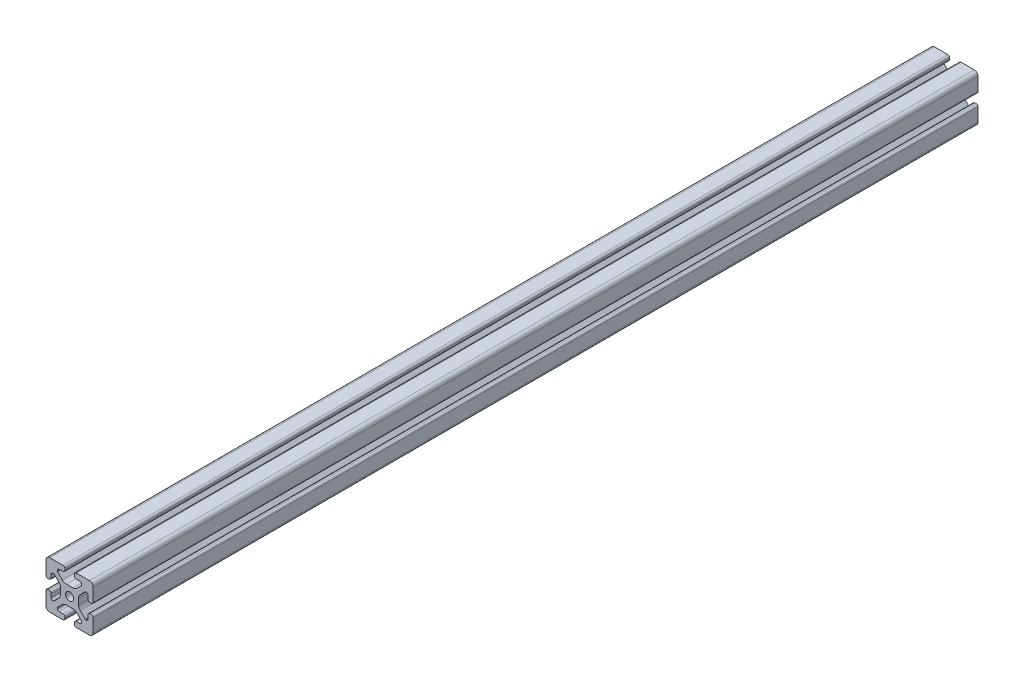
SolidWorks part; units mm, degrees
ref_plane "Front Plane" through (0, 0, 0) normal (0, 0, 1) x (1, 0, 0)
ref_plane "Top Plane" through (0, 0, 0) normal (0, 1, 0) x (1, 0, 0)
ref_plane "Right Plane" through (0, 0, 0) normal (1, 0, 0) x (0, 0, -1)
sketch "Sketch1" plane through (0, 0, 0) normal (0, 0, 1) x (1, 0, 0)
  line L0 (0, 19.7407) -> (0, -19.7407) construction
  line L1 (19.0335, 0) -> (-20.7246, 0) construction
  line L2 (-8.715, -15.5246) -> (-5.63, -15.5246)
  line L3 (-10.285, -13.9546) -> (-10.285, -13.4925)
  line L4 (-6.2171, -9.1098) -> (-10.0624, -12.9551)
  line L5 (2.7773, -7.685) -> (-2.7773, -7.685)
  line L6 (10.0624, -12.9551) -> (6.2171, -9.1098)
  line L7 (10.285, -13.9546) -> (10.285, -13.4925)
  line L8 (5.63, -15.5246) -> (8.715, -15.5246)
  line L9 (4.06, -18.43) -> (4.06, -17.0946)
  line L10 (-4.06, -18.43) -> (-4.06, -17.0946)
  line L11 (15.68, -8.7154) -> (15.68, -5.63)
  line L12 (-14.11, -10.2854) -> (-13.8169, -10.2854)
  line L13 (20, -16.83) -> (20, -5.63)
  line L14 (20, 5.63) -> (20, 13.0011)
  line L15 (-16.83, 20) -> (-5.63, 20)
  line L16 (5.63, 20) -> (12.9796, 20)
  line L17 (-8.715, 15.5246) -> (-5.63, 15.5246)
  line L18 (-20, -17.0184) -> (-20, -5.7579)
  line L19 (-20, 5.573) -> (-20, 13.0045)
  line L20 (-15.68, -8.7154) -> (-15.68, -5.7579)
  line L21 (-16.6746, -20) -> (-5.63, -20)
  line L22 (5.63, -20) -> (13, -20)
  line L23 (14.11, -10.2854) -> (13.6201, -10.2854)
  line L24 (13.1637, -9.947) -> (9.0762, -5.8595)
  line L25 (7.685, -2.5008) -> (7.685, 2.5008)
  line L26 (9.0762, 5.8595) -> (13.2795, 10.0628)
  line L27 (13.8169, 10.2854) -> (14.11, 10.2854)
  line L28 (15.68, 8.7154) -> (15.68, 5.63)
  line L29 (17.25, 4.06) -> (18.43, 4.06)
  line L30 (20, 13.0011) -> (20, 16.83)
  line L31 (16.83, 20) -> (12.9796, 20)
  line L32 (4.06, 18.43) -> (4.06, 17.0946)
  line L33 (5.63, 15.5246) -> (8.715, 15.5246)
  line L34 (10.285, 13.9546) -> (10.285, 13.4925)
  line L35 (10.0624, 12.9551) -> (6.2171, 9.1098)
  line L36 (2.7773, 7.685) -> (-2.7773, 7.685)
  line L37 (-6.2171, 9.1098) -> (-10.0624, 12.9551)
  line L38 (-10.285, 13.4925) -> (-10.285, 13.9546)
  line L39 (-4.06, 17.0946) -> (-4.06, 18.43)
  line L40 (-20, 16.83) -> (-20, 13.0045)
  line L41 (-18.43, 4.003) -> (-17.25, 4.003)
  line L42 (-15.68, 5.573) -> (-15.68, 8.4757)
  line L43 (-14.0552, 10.0447) -> (-13.7199, 10.033)
  line L44 (-13.0405, 9.8238) -> (-9.0762, 5.8595)
  line L45 (-7.685, 2.5008) -> (-7.685, -2.5008)
  line L46 (-9.0762, -5.8595) -> (-13.2795, -10.0628)
  line L47 (-17.2485, -4.1204) -> (-18.43, -4.1204)
  line L48 (13, -20) -> (16.83, -20)
  line L49 (18.43, -4.06) -> (17.25, -4.06)
  arc A0 (-5.63, -15.5246) -> (-4.06, -17.0946) centre (-5.63, -17.0946) cw
  arc A1 (-8.715, -15.5246) -> (-10.285, -13.9546) centre (-8.715, -13.9546) cw
  arc A2 (-10.285, -13.4925) -> (-10.0624, -12.9551) centre (-9.525, -13.4925) cw
  arc A3 (-6.2171, -9.1098) -> (-2.7773, -7.685) centre (-2.7773, -12.5496) cw
  arc A4 (2.7773, -7.685) -> (6.2171, -9.1098) centre (2.7773, -12.5496) cw
  arc A5 (10.0624, -12.9551) -> (10.285, -13.4925) centre (9.525, -13.4925) cw
  arc A6 (10.285, -13.9546) -> (8.715, -15.5246) centre (8.715, -13.9546) cw
  arc A7 (4.06, -17.0946) -> (5.63, -15.5246) centre (5.63, -17.0946) cw
  arc A8 (5.63, -20) -> (4.06, -18.43) centre (5.63, -18.43) cw
  arc A9 (-4.06, -18.43) -> (-5.63, -20) centre (-5.63, -18.43) cw
  circle A10 centre (0, 0) radius 3.4
  arc A11 (17.25, -4.06) -> (15.68, -5.63) centre (17.25, -5.63) ccw
  arc A12 (14.11, -10.2854) -> (15.68, -8.7154) centre (14.11, -8.7154) ccw
  arc A13 (13.1637, -9.947) -> (13.6201, -10.2854) centre (13.8117, -9.55) ccw
  arc A14 (7.685, -2.5008) -> (9.0762, -5.8595) centre (12.435, -2.5008) ccw
  arc A15 (9.0762, 5.8595) -> (7.685, 2.5008) centre (12.435, 2.5008) ccw
  arc A16 (13.8169, 10.2854) -> (13.2795, 10.0628) centre (13.8169, 9.5254) ccw
  arc A17 (15.68, 8.7154) -> (14.11, 10.2854) centre (14.11, 8.7154) ccw
  arc A18 (15.68, 5.63) -> (17.25, 4.06) centre (17.25, 5.63) ccw
  arc A19 (18.43, 4.06) -> (20, 5.63) centre (18.43, 5.63) ccw
  arc A20 (20, 16.83) -> (16.83, 20) centre (16.83, 16.83) ccw
  arc A21 (5.63, 20) -> (4.06, 18.43) centre (5.63, 18.43) ccw
  arc A22 (4.06, 17.0946) -> (5.63, 15.5246) centre (5.63, 17.0946) ccw
  arc A23 (10.285, 13.9546) -> (8.715, 15.5246) centre (8.715, 13.9546) ccw
  arc A24 (10.0624, 12.9551) -> (10.285, 13.4925) centre (9.525, 13.4925) ccw
  arc A25 (2.7773, 7.685) -> (6.2171, 9.1098) centre (2.7773, 12.5496) ccw
  arc A26 (-6.2171, 9.1098) -> (-2.7773, 7.685) centre (-2.7773, 12.5496) ccw
  arc A27 (-10.285, 13.4925) -> (-10.0624, 12.9551) centre (-9.525, 13.4925) ccw
  arc A28 (-8.715, 15.5246) -> (-10.285, 13.9546) centre (-8.715, 13.9546) ccw
  arc A29 (-5.63, 15.5246) -> (-4.06, 17.0946) centre (-5.63, 17.0946) ccw
  arc A30 (-4.06, 18.43) -> (-5.63, 20) centre (-5.63, 18.43) ccw
  arc A31 (-16.83, 20) -> (-20, 16.83) centre (-16.83, 16.83) ccw
  arc A32 (-20, 5.573) -> (-18.43, 4.003) centre (-18.43, 5.573) ccw
  arc A33 (-17.25, 4.003) -> (-15.68, 5.573) centre (-17.25, 5.573) ccw
  arc A34 (-14.0552, 10.0447) -> (-15.68, 8.4757) centre (-14.11, 8.4757) ccw
  arc A35 (-13.0405, 9.8238) -> (-13.7199, 10.033) centre (-13.5779, 9.2864) ccw
  arc A36 (-7.685, 2.5008) -> (-9.0762, 5.8595) centre (-12.435, 2.5008) ccw
  arc A37 (-9.0762, -5.8595) -> (-7.685, -2.5008) centre (-12.435, -2.5008) ccw
  arc A38 (-13.8169, -10.2854) -> (-13.2795, -10.0628) centre (-13.8169, -9.5254) ccw
  arc A39 (-15.68, -8.7154) -> (-14.11, -10.2854) centre (-14.11, -8.7154) ccw
  arc A40 (-15.68, -5.7579) -> (-17.2485, -4.1204) centre (-17.2485, -5.6904) ccw
  arc A41 (-18.43, -4.1204) -> (-20, -5.7579) centre (-18.4315, -5.6904) ccw
  arc A42 (-20, -17.0184) -> (-16.6746, -20) centre (-16.8354, -16.8341) ccw
  arc A43 (16.83, -20) -> (20, -16.83) centre (16.83, -16.83) ccw
  arc A44 (20, -5.63) -> (18.43, -4.06) centre (18.43, -5.63) ccw
  dimension "D1" = 6.8
  dimension "D2" = 4.32
  dimension "D3" = 15.37
  dimension "D4" = 20.57
  dimension "D5" = 15.37
  dimension "D6" = 40
  dimension "D7" = 20
  dimension "D8" = 4.32
  dimension "D9" = 8.12
extrude "Boss-Extrude1" add sketch "Sketch1" along normal blind 750
